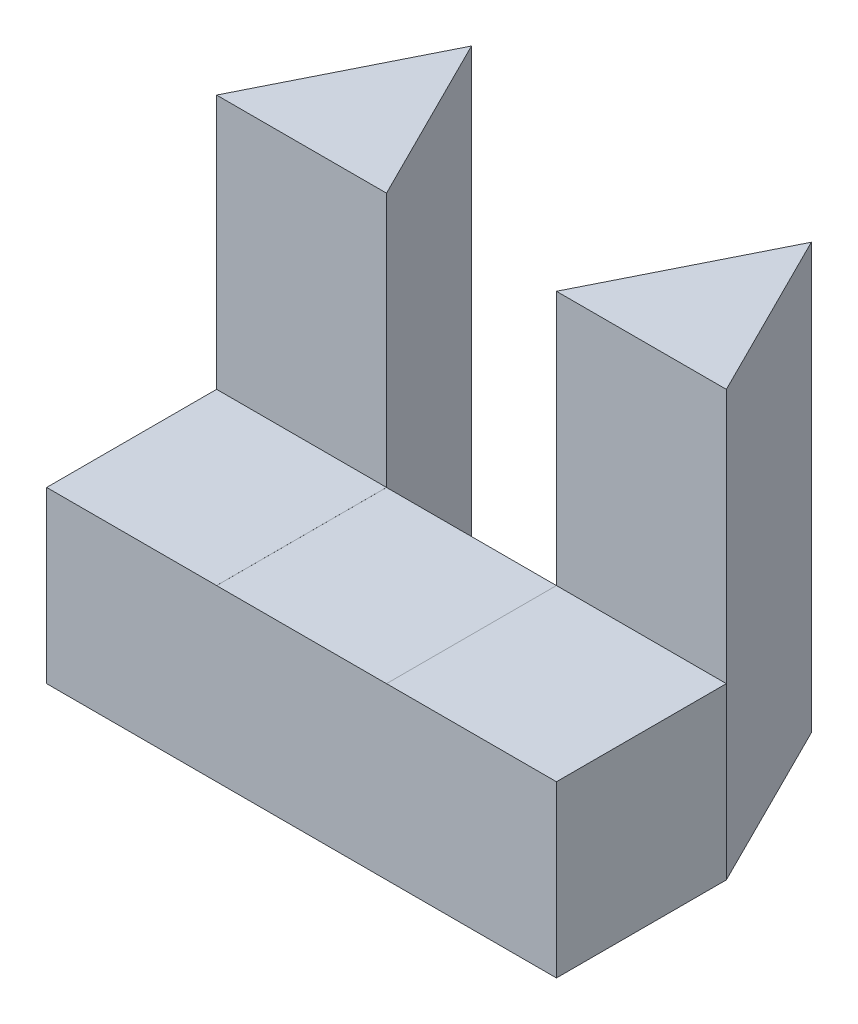
SolidWorks part; units mm, degrees
ref_plane "Front Plane" through (0, 0, 0) normal (0, 0, 1) x (1, 0, 0)
ref_plane "Top Plane" through (0, 0, 0) normal (0, 1, 0) x (1, 0, 0)
ref_plane "Right Plane" through (0, 0, 0) normal (1, 0, 0) x (0, 0, -1)
sketch "Sketch1" plane through (0, 0, 0) normal (0, 1, 0) x (1, 0, 0)
  line L0 (0, 0) -> (6, 0)
  line L1 (6, 0) -> (6, 2)
  line L2 (5, 4) -> (4, 2)
  line L3 (4, 2) -> (2, 2)
  line L4 (2, 2) -> (1, 4)
  line L5 (1, 4) -> (0, 2)
  line L6 (0, 2) -> (0, 0)
  line L7 (6, 2) -> (5, 4)
  dimension "D1" = 6
  dimension "D2" = 2
  dimension "D3" = 2
  dimension "D4" = 2
  dimension "D5" = 2
  dimension "D6" = 2
  dimension "D7" = 2
  dimension "D8" = 1
  dimension "D9" = 2
  dimension "D10" = 1
extrude "Boss-Extrude1" add sketch "Sketch1" along normal blind 5
sketch "Sketch2" plane through (0, 0, 0) normal (0, 0, 1) x (1, 0, 0)
  line L0 (4, 5) -> (4, 0) construction
  line L1 (2, 5) -> (4, 5)
  line L2 (2, 5) -> (2, 2)
  line L3 (2, 2) -> (4, 2)
  line L4 (4, 5) -> (4, 2)
  dimension "D1" = 3
extrude "Cut-Extrude1" cut sketch "Sketch2" against normal blind 5
sketch "Sketch3" plane through (0, 0, 0) normal (-1, 0, 0) x (0, 0, 1)
  line L0 (0, 5) -> (0, 0) construction
  line L1 (-2, 5) -> (0, 5)
  line L2 (-2, 5) -> (-2, 2.0004)
  line L3 (-2, 2.0004) -> (0, 2.0004)
  line L4 (0, 5) -> (0, 2.0004)
extrude "Cut-Extrude2" cut sketch "Sketch3" against normal blind 15
